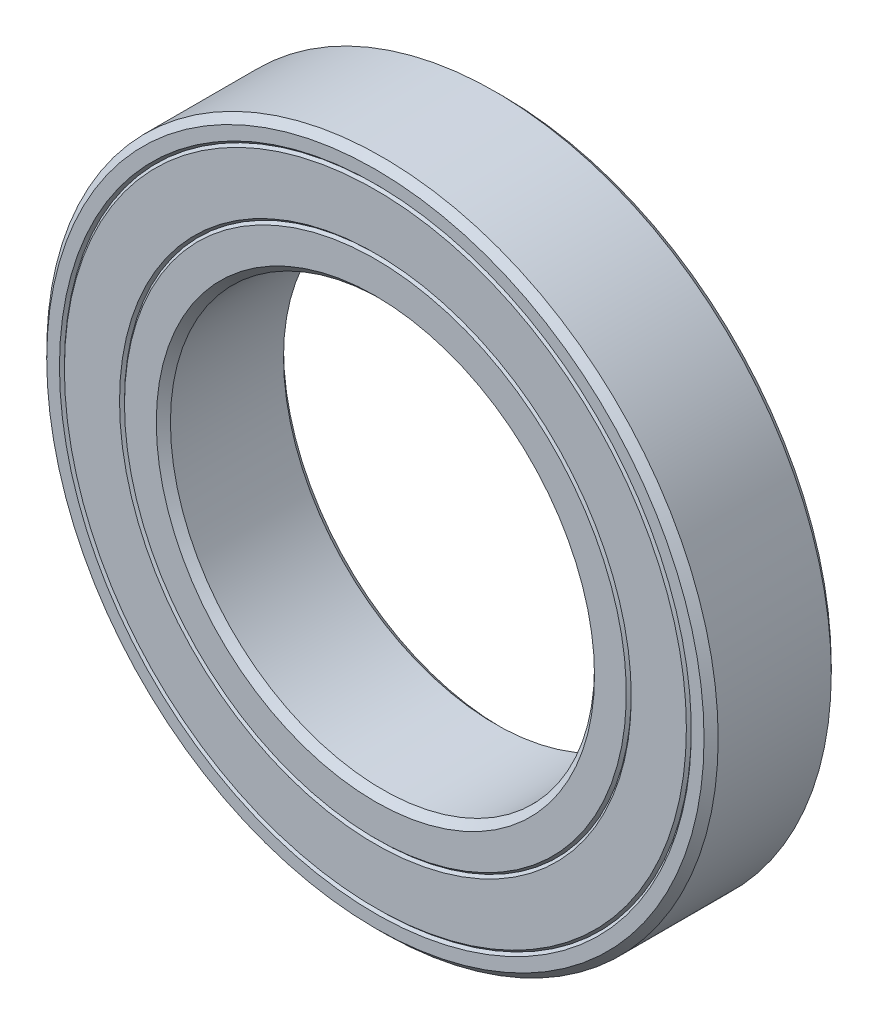
SolidWorks part; units mm, degrees
ref_plane "Front Plane" through (0, 0, 0) normal (0, 0, 1) x (1, 0, 0)
ref_plane "Top Plane" through (0, 0, 0) normal (0, 1, 0) x (1, 0, 0)
ref_plane "Right Plane" through (0, 0, 0) normal (1, 0, 0) x (0, 0, -1)
sketch "Sketch1" plane through (0, 0, 0) normal (0, 0, 1) x (1, 0, 0)
  circle A0 centre (0, 0) radius 47.5
  circle A1 centre (0, 0) radius 30
  dimension "D1" = 95
  dimension "D2" = 60
extrude "Extrude1" add sketch "Sketch1" along normal blind 18
chamfer "Chamfer1" distance 1 angle 45 4 edges at (30, 0, 0) (30, 0, 18) (47.5, 0, 0) (47.5, 0, 18)
sketch "Sketch2" plane through (0, 0, 0) normal (1, 0, 0) x (0, 0, -1)
  line L0 (0, 0) -> (-18, 0) construction
  line L1 (0.2089, 30) -> (-39.5699, 30) construction
  line L2 (-18, 35.5) -> (-17.65, 35.85)
  line L4 (-18, 46.5) -> (-18, -46.5) construction
  line L5 (-17.65, 35.85) -> (-18, 36.2)
  line L6 (-18, 40.1) -> (-13.5691, 40.1) construction
  line L7 (-17.65, 44.35) -> (-18, 44)
  line L8 (-18, 44.7) -> (-17.65, 44.35)
  line L9 (-1, 47.5) -> (-17, 47.5) construction
  line L10 (-18, 35.5) -> (-18, 36.2)
  line L11 (-18, 44.7) -> (-18, 44)
  line L12 (-9, 0) -> (-9, 10.7064) construction
  line L13 (0, 35.5) -> (0, 36.2)
  line L14 (-0.35, 35.85) -> (0, 36.2)
  line L15 (0, 35.5) -> (-0.35, 35.85)
  line L16 (0, 44.7) -> (0, 44)
  line L17 (0, 44.7) -> (-0.35, 44.35)
  line L18 (-0.35, 44.35) -> (0, 44)
  dimension "D1" = 30
  dimension "D2" = 71
  dimension "D3" = 0.7
  dimension "D4" = 2.8
revolve "Cut-Revolve1" cut sketch "Sketch2" angle 360 about L0
